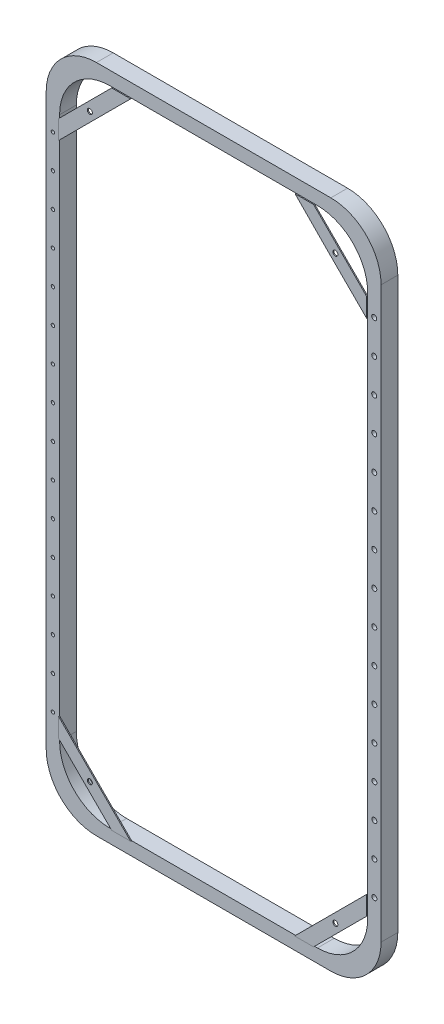
SolidWorks part; units mm, degrees
material "Ferro duttile"
ref_plane "Piano frontale" through (0, 0, 0) normal (0, 0, 1) x (1, 0, 0)
ref_plane "Piano superiore" through (0, 0, 0) normal (0, 1, 0) x (1, 0, 0)
ref_plane "Piano destro" through (0, 0, 0) normal (1, 0, 0) x (0, 0, -1)
sketch "Schizzo1" plane through (0, 0, 0) normal (0, 0, 1) x (1, 0, 0)
  line L0 (-500, 1000) -> (-204.5493, 1000)
  line L1 (-500, 1000) -> (500, 1000)
  line L2 (-500, 1000) -> (-500, -1000)
  line L3 (-500, -1000) -> (500, -1000)
  line L4 (500, 1000) -> (500, -1000)
  line L5 (-500, 1000) -> (500, -1000) construction
  line L6 (-500, -1000) -> (500, 1000) construction
  point P0 (0, 0)
  dimension "D1" = 2000
  dimension "D2" = 1000
extrude "Estrusione-Estrusione2" add sketch "Schizzo1" along normal blind 50 contours L4 L1 L0 L2 L3
fillet "Raccordo2" radius 150 4 edges at (-500, -1000, 25) (500, -1000, 25) (-500, 1000, 25) (500, 1000, 25)
sketch "Schizzo4" plane through (0, 0, 50) normal (0, 0, 1) x (1, 0, 0)
  line L0 (-350, 1000) -> (350, 1000) construction
  line L1 (-310, 960) -> (310, 960)
  line L2 (-460, 810) -> (-460, -810)
  line L3 (-310, -960) -> (310, -960)
  line L4 (460, 810) -> (460, -810)
  line L5 (-460, 960) -> (316.3137, -660.1329) construction
  line L7 (500, 850) -> (500, -850) construction
  line L8 (-500, 850) -> (-500, -850) construction
  line L9 (-350, -1000) -> (350, -1000) construction
  line L14 (-316.3137, -660.1329) -> (316.3137, 660.1329) construction
  arc A0 (-310, 960) -> (-460, 810) centre (-310, 810) ccw
  arc A1 (460, 810) -> (310, 960) centre (310, 810) ccw
  arc A2 (-460, -810) -> (-310, -960) centre (-310, -810) ccw
  arc A3 (310, -960) -> (460, -810) centre (310, -810) ccw
  point P0 (0, 0)
  dimension "D1" = 40
  dimension "D2" = 40
  dimension "D3" = 40
  dimension "D4" = 40
  dimension "D5" = 150
  dimension "D6" = 150
  dimension "D7" = 150
  dimension "D8" = 150
  dimension "D9" = 150
extrude "Taglio-Estrusione2" cut sketch "Schizzo4" against normal blind 50
sketch "Schizzo7" plane through (0, 0, 50) normal (0, 0, 1) x (1, 0, 0)
  line L0 (380.7107, 880.7107) -> (460, 801.4214)
  line L1 (246.5016, 960) -> (301.4214, 960)
  line L2 (460, -810) -> (460, 810) construction
  line L4 (380.7107, 880.7107) -> (301.4214, 960)
  line L6 (310, 960) -> (-310, 960) construction
  line L7 (460, 744.8528) -> (460, 801.4214)
  line L8 (352.4264, 852.4264) -> (460, 744.8528)
  line L9 (352.4264, 852.4264) -> (246.5016, 960)
  dimension "D2" = 40
extrude "Estrusione-Estrusione5" add sketch "Schizzo7" along normal blind 3 separate body
sketch "Schizzo8" plane through (0, 0, 50) normal (0, 0, 1) x (1, 0, 0)
  line L0 (-416.066, 916.066) -> (-380.7107, 880.7107)
  line L1 (-380.7107, 880.7107) -> (-301.4214, 960)
  line L2 (310, 960) -> (-310, 960) construction
  line L3 (-380.7107, 880.7107) -> (-460, 801.4214)
  line L4 (-460, 810) -> (-460, -810) construction
  line L5 (-380.7107, 880.7107) -> (-352.4264, 852.4264)
  line L6 (-352.4264, 852.4264) -> (-244.8528, 960)
  line L7 (-352.4264, 852.4264) -> (-460, 744.8528)
  arc A1 (-310, 960) -> (-460, 810) centre (-310, 810) ccw construction
  line M2 (-310, 960) -> (310, 960)
  line M8 (-460, -810) -> (-460, 810)
  dimension "D1" = 50
  dimension "D2" = 40
extrude "Estrusione-Estrusione6" add sketch "Schizzo8" along normal blind 3 separate body contours L5 L6 L1 M2 | L7 L5 L3 M8
sketch "Schizzo9" plane through (0, 0, 50) normal (0, 0, 1) x (1, 0, 0)
  line L0 (-416.066, -916.066) -> (-380.7107, -880.7107)
  line L1 (-380.7107, -880.7107) -> (-460, -801.4214)
  line L2 (-460, 810) -> (-460, -810) construction
  line L3 (-380.7107, -880.7107) -> (-301.4214, -960)
  line L4 (-310, -960) -> (310, -960) construction
  line L6 (-273.1371, -931.7157) -> (-460, -744.8528)
  line L7 (-273.1371, -931.7157) -> (-244.8528, -960)
  arc A0 (-460, -810) -> (-310, -960) centre (-310, -810) ccw construction
  line M8 (310, -960) -> (-310, -960)
  line M10 (-460, -810) -> (-460, 810)
  dimension "D1" = 50
  dimension "D2" = 40
extrude "Estrusione-Estrusione7" add sketch "Schizzo9" along normal blind 3 separate body contours L7 L6 L1 L3 M10 M8
sketch "Schizzo10" plane through (0, 0, 50) normal (0, 0, 1) x (1, 0, 0)
  line L0 (416.066, -916.066) -> (380.7107, -880.7107)
  line L1 (380.7107, -880.7107) -> (301.4214, -960)
  line L2 (-310, -960) -> (310, -960) construction
  line L3 (380.7107, -880.7107) -> (460, -801.4214)
  line L4 (460, -810) -> (460, 810) construction
  line L5 (352.4264, -852.4264) -> (244.8528, -960)
  line L6 (352.4264, -852.4264) -> (460, -744.8528)
  arc A1 (310, -960) -> (460, -810) centre (310, -810) ccw construction
  line M6 (460, 810) -> (460, -810)
  line M8 (310, -960) -> (-310, -960)
  dimension "D1" = 50
  dimension "D2" = 40
extrude "Estrusione-Estrusione8" add sketch "Schizzo10" along normal blind 3 separate body contours L6 L5 L1 L3 M8 M6
sketch "Schizzo11" plane through (0, 0, 53) normal (0, 0, 1) x (1, 0, 0)
  line L0 (-352.4264, 852.4264) -> (-366.5685, 866.5685)
  line L1 (-460, 744.8528) -> (-244.8528, 960) construction
  circle A0 centre (-366.5685, 866.5685) radius 7.5
  dimension "D1" = 15
  dimension "D2" = 20
extrude "Taglio-Estrusione3" cut sketch "Schizzo11" against normal through all
sketch "Schizzo12" plane through (0, 0, 53) normal (0, 0, 1) x (1, 0, 0)
  line L0 (246.5016, 960) -> (352.4264, 852.4264) construction
  circle A0 centre (366.5644, 866.5736) radius 7.5
  dimension "D1" = 15
  dimension "D2" = 20
extrude "Taglio-Estrusione4" cut sketch "Schizzo12" against normal through all
sketch "Schizzo13" plane through (0, 0, 53) normal (0, 0, 1) x (1, 0, 0)
  line L0 (-460, -744.8528) -> (-244.8528, -960) construction
  circle A0 centre (-366.5685, -866.5685) radius 7.5
  point P4 (-352.4264, -852.4264)
  dimension "D1" = 15
  dimension "D2" = 20
extrude "Taglio-Estrusione5" cut sketch "Schizzo13" against normal through all
sketch "Schizzo14" plane through (0, 0, 53) normal (0, 0, 1) x (1, 0, 0)
  line L0 (244.8528, -960) -> (460, -744.8528) construction
  circle A0 centre (366.5685, -866.5685) radius 7.5
  dimension "D1" = 15
  dimension "D2" = 20
extrude "Taglio-Estrusione6" cut sketch "Schizzo14" against normal through all
sketch "Schizzo15" plane through (0, 0, 50) normal (0, 0, 1) x (1, 0, 0)
  line L0 (460, -810) -> (460, 810) construction
  circle A0 centre (480, -744.8528) radius 7.5
  circle A1 centre (479.972, -644.8528) radius 7.5
  circle A2 centre (479.9441, -544.8528) radius 7.5
  circle A3 centre (479.9161, -444.8528) radius 7.5
  circle A4 centre (479.8882, -344.8528) radius 7.5
  circle A5 centre (479.8602, -244.8528) radius 7.5
  circle A6 centre (479.8322, -144.8528) radius 7.5
  circle A7 centre (479.8043, -44.8528) radius 7.5
  circle A8 centre (479.7763, 55.1472) radius 7.5
  circle A9 centre (479.7483, 155.1472) radius 7.5
  circle A10 centre (479.7204, 255.1471) radius 7.5
  circle A11 centre (479.6924, 355.1471) radius 7.5
  circle A12 centre (479.6645, 455.1471) radius 7.5
  circle A13 centre (479.6365, 555.1471) radius 7.5
  circle A14 centre (479.6085, 655.1471) radius 7.5
  circle A15 centre (479.5806, 755.1471) radius 7.5
  dimension "D1" = 15
  dimension "D2" = 20
  dimension "D3" = 16
extrude "Taglio-Estrusione7" cut sketch "Schizzo15" against normal through all
sketch "Schizzo16" plane through (0, 0, 50) normal (0, 0, 1) x (1, 0, 0)
  circle A0 centre (-480, -744.8528) radius 5
  circle A1 centre (-480, -644.8528) radius 5
  circle A2 centre (-480, -544.8528) radius 5
  circle A3 centre (-480, -444.8528) radius 5
  circle A4 centre (-480, -344.8528) radius 5
  circle A5 centre (-480, -244.8528) radius 5
  circle A6 centre (-480, -144.8528) radius 5
  circle A7 centre (-480, -44.8528) radius 5
  circle A8 centre (-480, 55.1472) radius 5
  circle A9 centre (-480, 155.1472) radius 5
  circle A10 centre (-480, 255.1472) radius 5
  circle A11 centre (-480, 355.1472) radius 5
  circle A12 centre (-480, 455.1472) radius 5
  circle A13 centre (-480, 555.1472) radius 5
  circle A14 centre (-480, 655.1472) radius 5
  circle A15 centre (-480, 755.1472) radius 5
  dimension "D1" = 10
  dimension "D2" = 16
extrude "Taglio-Estrusione9" cut sketch "Schizzo16" against normal through all
